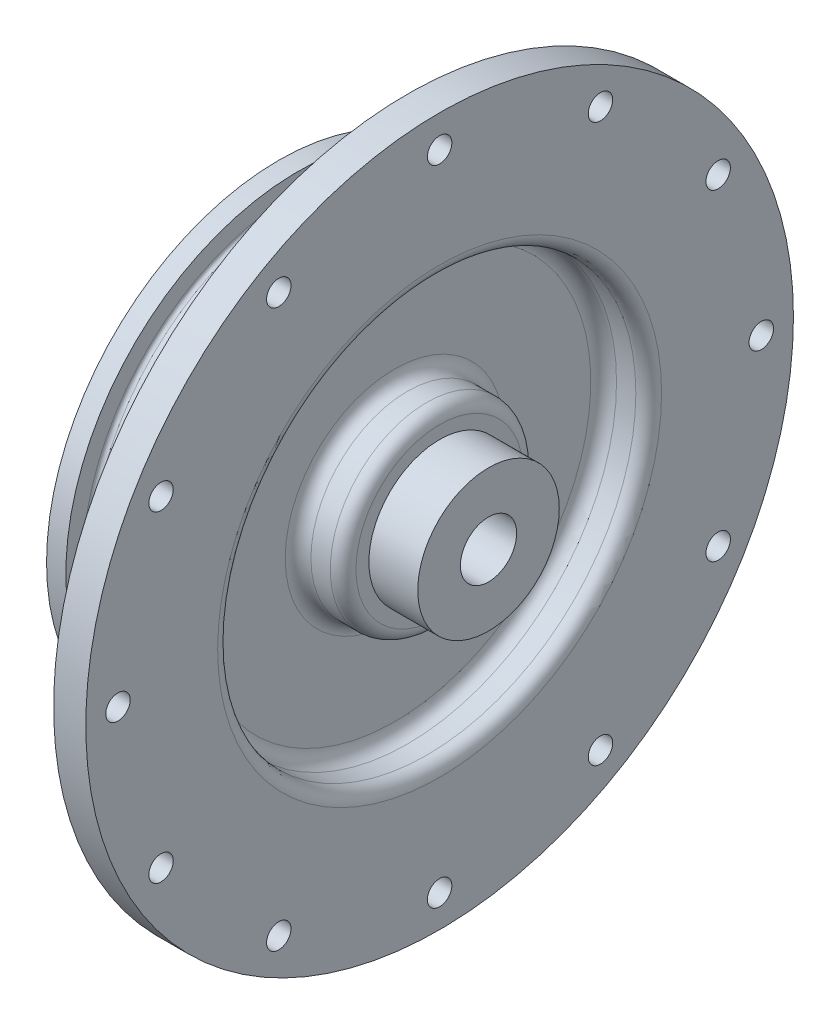
SolidWorks part; units mm, degrees
material "7075-T6 (SN)"
ref_plane "Front Plane" through (0, 0, 0) normal (0, 0, 1) x (1, 0, 0)
ref_plane "Top Plane" through (0, 0, 0) normal (0, 1, 0) x (1, 0, 0)
ref_plane "Right Plane" through (0, 0, 0) normal (1, 0, 0) x (0, 0, -1)
sketch "Sketch1" plane through (0, 0, 0) normal (1, 0, 0) x (0, 0, -1)
  circle A0 centre (0, 0) radius 69.85
  dimension "D1" = 139.7
extrude "Boss-Extrude1" add sketch "Sketch1" along normal blind 6.35
sketch "Sketch2" plane through (0, 0, 0) normal (-1, 0, 0) x (0, 0, 1)
  circle A0 centre (0, 0) radius 45.847
  dimension "D1" = 91.694
extrude "Boss-Extrude2" add sketch "Sketch2" along normal blind 25.4
sketch "Sketch10" plane through (0, 0, 0) normal (0, 1, 0) x (1, 0, 0)
  line L0 (0, 0) -> (-53.2238, 0) construction
  line L1 (-26.2636, 0) -> (26.2636, 0) construction
  line L2 (0, 0) -> (0, 64.5447) construction
  line L3 (0, -62.865) -> (0, 62.865) construction
ref_plane "Plane1" through (0, 0, -45.847) normal (0, 0, -1) x (-1, 0, 0)
sketch "Sketch11" plane through (0, 0, -45.847) normal (0, 0, -1) x (-1, 0, 0)
  line L0 (0, 0) -> (53.2238, 0) construction
  line L1 (0, -45.847) -> (0, 45.847) construction
  circle A0 centre (7.62, 0) radius 1.8986
  dimension "D2" = 3.7973
  dimension "D1" = 7.62
extrude "Cut-Extrude3" cut sketch "Sketch11" against normal blind 10.16
pattern_circular "CirPattern1" count 12 over 360 about axis through (0, 0, 0) along (1, 0, 0) of "Cut-Extrude3"
sketch "Sketch15" plane through (6.35, 0, 0) normal (1, 0, 0) x (0, 0, -1)
  circle A0 centre (0, 0) radius 5.5562
  dimension "D1" = 11.1125
extrude "Cut-Extrude4" cut sketch "Sketch15" against normal through all both and the other way through all
sketch "Sketch16" plane through (0, 0, 0) normal (0, 0, 1) x (1, 0, 0)
  line L0 (-9.5186, 45.847) -> (-25.4, 45.847) construction
  line L1 (-21.59, 45.847) -> (-14.4018, 45.847)
  line L2 (-21.59, 45.847) -> (-21.59, 42.4815)
  line L3 (-20.828, 41.7195) -> (-15.1638, 41.7195)
  line L4 (-14.4018, 45.847) -> (-14.4018, 42.4815)
  line L5 (0, 0) -> (-53.2238, 0) construction
  line L6 (-25.4, 45.847) -> (-25.4, -45.847) construction
  arc A0 (-14.4018, 42.4815) -> (-15.1638, 41.7195) centre (-15.1638, 42.4815) cw
  arc A1 (-20.828, 41.7195) -> (-21.59, 42.4815) centre (-20.828, 42.4815) cw
  point P8 (-26.6119, 0)
  point P13 (-14.4018, 41.7195)
  point P16 (-21.59, 41.7195)
  dimension "D4" = 0.762
  dimension "D1" = 41.7195
  dimension "D2" = 3.81
  dimension "D3" = 7.1882
revolve "Cut-Revolve1" cut sketch "Sketch16" angle 360 about L0
sketch "Sketch17" plane through (6.35, 0, 0) normal (1, 0, 0) x (0, 0, -1)
  circle A0 centre (0, 0) radius 13.97
  circle A1 centre (0, 0) radius 5.5562
  dimension "D1" = 27.94
  dimension "D2" = 11.1125
extrude "Boss-Extrude3" add sketch "Sketch17" along normal blind 9.652
cosmetic thread "Cosmetic Thread1" parameters "D2"=23.1953
sketch "Sketch18" plane through (0, 0, 0) normal (0, 0, 1) x (1, 0, 0)
  line L0 (6.35, -69.85) -> (6.35, 69.85) construction
  line L1 (6.35, 41.275) -> (-2.54, 41.275)
  line L2 (6.35, 41.275) -> (6.35, 19.05)
  line L3 (6.35, 19.05) -> (-2.54, 19.05)
  line L4 (-2.54, 41.275) -> (-2.54, 19.05)
  line L5 (0, 0) -> (-53.2238, 0) construction
  dimension "D1" = 8.89
  dimension "D2" = 19.05
  dimension "D3" = 41.275
revolve "Cut-Revolve2" cut sketch "Sketch18" angle 360 about L0
fillet "Fillet1" radius 2.54 4 edges at (6.35, 0, -41.275) (-2.54, 0, -41.275) (-2.54, 0, -19.05) (6.35, 0, -19.05)
sketch "Sketch19" plane through (6.35, 0, 0) normal (1, 0, 0) x (0, 0, -1)
  line L0 (0, 0) -> (0, 63.5) construction
  circle A0 centre (0, 0) radius 57.15 construction
  circle A1 centre (0, 0) radius 63.5 construction
  circle A2 centre (0, 63.5) radius 2.413
  circle A3 centre (31.75, 54.9926) radius 2.413
  circle A4 centre (54.9926, 31.75) radius 2.413
  circle A5 centre (63.5, 0) radius 2.413
  circle A6 centre (54.9926, -31.75) radius 2.413
  circle A7 centre (31.75, -54.9926) radius 2.413
  circle A8 centre (0, -63.5) radius 2.413
  circle A9 centre (-31.75, -54.9926) radius 2.413
  circle A10 centre (-54.9926, -31.75) radius 2.413
  circle A11 centre (-63.5, 0) radius 2.413
  circle A12 centre (-54.9926, 31.75) radius 2.413
  circle A13 centre (-31.75, 54.9926) radius 2.413
  point P30 (0, 0)
  dimension "D1" = 114.3
  dimension "D2" = 127
  dimension "D3" = 4.826
  dimension "D4" = 12
extrude "Cut-Extrude5" cut sketch "Sketch19" against normal through all
